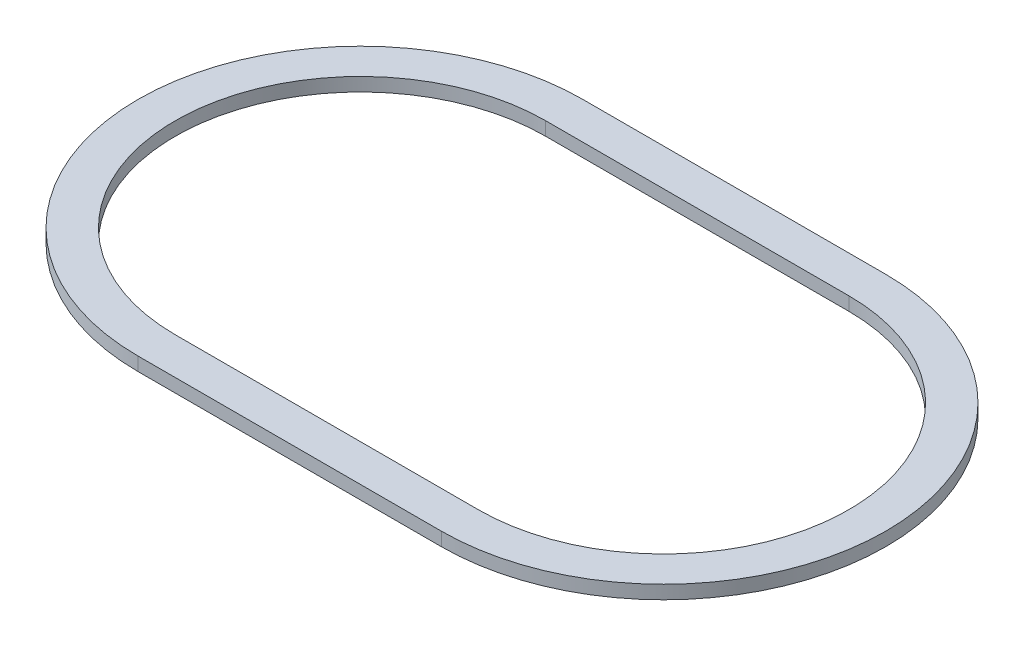
SolidWorks part; units mm, degrees
material "Резина"
ref_plane "Спереди" through (0, 0, 0) normal (0, 0, 1) x (1, 0, 0)
ref_plane "Сверху" through (0, 0, 0) normal (0, 1, 0) x (1, 0, 0)
ref_plane "Справа" through (0, 0, 0) normal (1, 0, 0) x (0, 0, -1)
sketch "Эскиз1" plane through (0, 0, 0) normal (0, 1, 0) x (1, 0, 0)
  line L0 (-22.5, 33) -> (22.5, 33)
  line L1 (-22.5, -33) -> (22.5, -33)
  line L2 (0, 0) -> (0, 33) construction
  arc A0 (-22.5, 33) -> (-22.5, -33) centre (-22.5, 0) ccw
  arc A1 (22.5, -33) -> (22.5, 33) centre (22.5, 0) ccw
  point P8 (-55.5, 0)
  point P9 (55.5, 0)
  dimension "D1" = 66
  dimension "D3" = 111
extrude "Бобышка-Вытянуть1" add sketch "Эскиз1" along normal blind 2
sketch "Эскиз2" plane through (0, 2, 0) normal (0, 1, 0) x (1, 0, 0)
  line L0 (-22.5, 27.5) -> (22.5, 27.5)
  line L1 (-22.5, -27.5) -> (22.5, -27.5)
  line L2 (0, 0) -> (0, 27.5) construction
  arc A0 (-22.5, 27.5) -> (-22.5, -27.5) centre (-22.5, 0) ccw
  arc A1 (22.5, -27.5) -> (22.5, 27.5) centre (22.5, 0) ccw
  point P6 (-50, 0)
  point P7 (50, 0)
  dimension "D1" = 55
  dimension "D2" = 100
extrude "Вырез-Вытянуть1" cut sketch "Эскиз2" against normal through all
